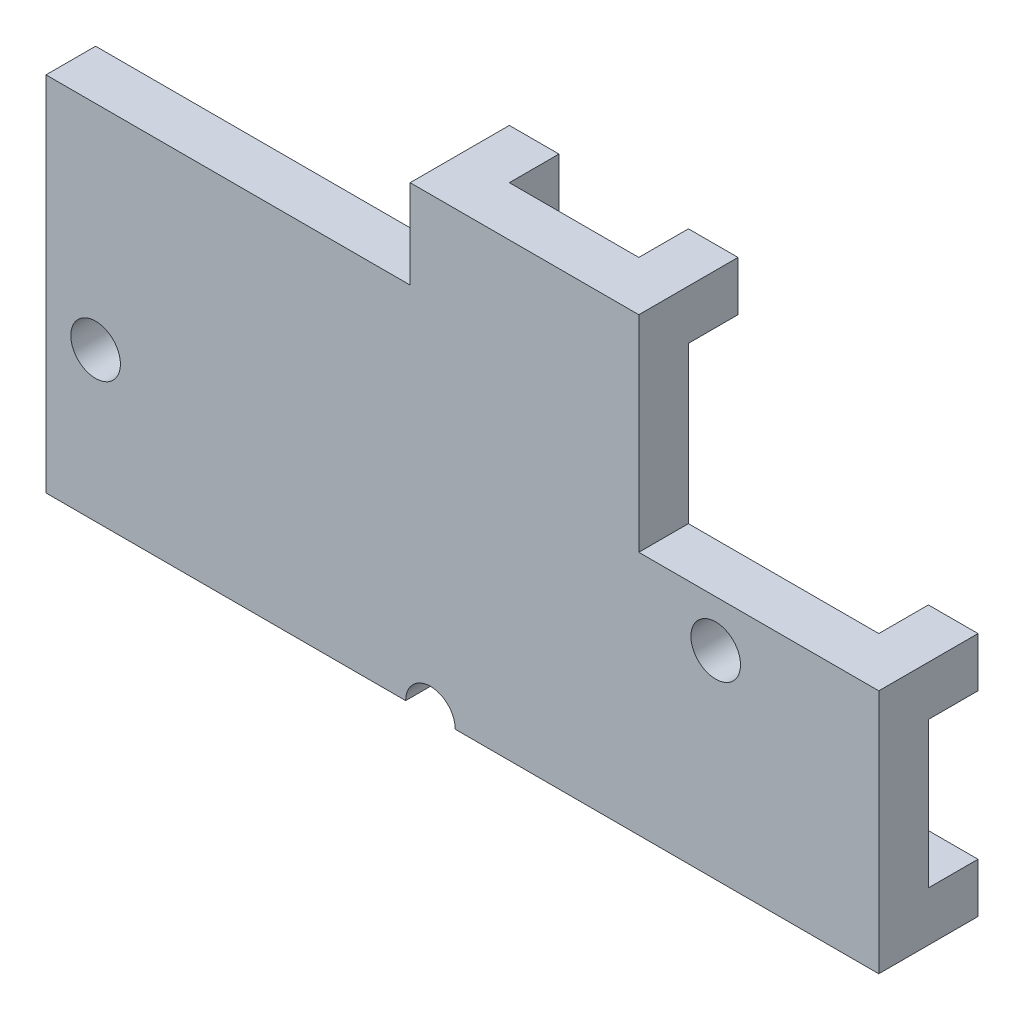
SolidWorks part; units mm, degrees
ref_plane "Front Plane" through (0, 0, 0) normal (0, 0, 1) x (1, 0, 0)
ref_plane "Top Plane" through (0, 0, 0) normal (0, 1, 0) x (1, 0, 0)
ref_plane "Right Plane" through (0, 0, 0) normal (1, 0, 0) x (0, 0, -1)
sketch "Sketch1" plane through (0, 0, 0) normal (0, 0, 1) x (1, 0, 0)
  line L1 (80.5727, -2.7261) -> (95.5727, -2.7261)
  line L2 (80.5727, -2.7261) -> (80.5727, -10.0261)
  line L3 (80.5727, -10.0261) -> (95.5727, -10.0261)
  line L4 (95.5727, -2.7261) -> (95.5727, -10.0261)
  dimension "D1" = 7.3
  dimension "D2" = 15
extrude "Boss-Extrude1" add sketch "Sketch1" along normal blind 1
sketch "Sketch2" plane through (0, 0, 1) normal (0, 0, 1) x (1, 0, 0)
  line L1 (95.5727, -2.7261) -> (92.5227, -2.7261)
  line L2 (95.5727, -2.7261) -> (95.5727, -5.0861)
  line L3 (95.5727, -5.0861) -> (92.5227, -5.0861)
  line L4 (92.5227, -2.7261) -> (92.5227, -5.0861)
extrude "Cut-Extrude1" cut sketch "Sketch2" against normal blind 1
sketch "Sketch5" plane through (95.5727, 0, 0) normal (1, 0, 0) x (0, 0, -1)
  line L1 (0, -10.0261) -> (-1, -10.0261)
  line L2 (0, -10.0261) -> (0, -5.0861)
  line L3 (0, -5.0861) -> (-1, -5.0861)
  line L4 (-1, -10.0261) -> (-1, -5.0861)
extrude ":ength-Extrude" add sketch "Sketch5" along normal blind 1.7874
sketch "Sketch6" plane through (0, -2.7261, 0) normal (0, 1, 0) x (1, 0, 0)
  line L0 (92.5227, -1) -> (80.5727, -1) construction
  line L1 (92.5227, 0) -> (87.9127, 0)
  line L2 (92.5227, 0) -> (92.5227, -1)
  line L3 (92.5227, -1) -> (87.9127, -1)
  line L4 (87.9127, 0) -> (87.9127, -1)
extrude "Height-Extrude" add sketch "Sketch6" along normal blind 1.7874
sketch "Screws" plane through (0, 0, 0) normal (0, 0, -1) x (-1, 0, 0)
  line L0 (-80.5727, -10.0261) -> (-97.3601, -10.0261) construction
  line L2 (-80.5727, -2.7261) -> (-80.5727, -10.0261) construction
  line L5 (-87.9127, -2.7261) -> (-80.5727, -2.7261) construction
  line L9 (-80.5727, -10.0261) -> (-97.3601, -10.0261) construction
  line L10 (-80.5727, -2.7261) -> (-80.5727, -10.0261) construction
  circle A0 centre (-81.5727, -7.0261) radius 0.5
  circle A1 centre (-88.3227, -10.0261) radius 0.5
  circle A2 centre (-94.0727, -6.0261) radius 0.5
  dimension "D1" = 1
  dimension "D2" = 1
  dimension "D3" = 3
  dimension "D5" = 7.3
  dimension "D4" = 1
  dimension "D6" = 7.75
  dimension "D7" = 1
  dimension "D8" = 13.5
  dimension "D9" = 4
extrude "Cut-Extrude2" cut sketch "Screws" against normal blind 1
sketch "Sketch8" plane through (0, 0, 0) normal (0, 0, -1) x (-1, 0, 0)
  line L1 (-91.5227, -1.9387) -> (-92.5227, -1.9387)
  line L2 (-91.5227, -1.9387) -> (-91.5227, -0.9387)
  line L3 (-91.5227, -0.9387) -> (-92.5227, -0.9387)
  line L4 (-92.5227, -1.9387) -> (-92.5227, -0.9387)
  line L5 (-87.9127, -1.9387) -> (-88.9127, -1.9387)
  line L6 (-87.9127, -1.9387) -> (-87.9127, -0.9387)
  line L7 (-87.9127, -0.9387) -> (-88.9127, -0.9387)
  line L8 (-88.9127, -1.9387) -> (-88.9127, -0.9387)
  line L9 (-87.9127, -1.9387) -> (-88.9127, -0.9387) construction
  line L10 (-87.9127, -0.9387) -> (-88.9127, -1.9387) construction
  line L11 (-96.3601, -6.0861) -> (-97.3601, -6.0861)
  line L12 (-96.3601, -6.0861) -> (-96.3601, -5.0861)
  line L13 (-96.3601, -5.0861) -> (-97.3601, -5.0861)
  line L14 (-97.3601, -6.0861) -> (-97.3601, -5.0861)
  line L15 (-96.3601, -9.0261) -> (-97.3601, -9.0261)
  line L16 (-96.3601, -9.0261) -> (-96.3601, -10.0261)
  line L17 (-96.3601, -10.0261) -> (-97.3601, -10.0261)
  line L18 (-97.3601, -9.0261) -> (-97.3601, -10.0261)
  line L23 (-87.9127, -0.9387) -> (-87.9127, -2.7261) construction
  point P5 (-88.4127, -1.4387)
  point P21 (0, 0)
  point P22 (0, 0)
  point P24 (0, 0)
  point P26 (0, 0)
  point P27 (0, 0)
extrude "Pins" add sketch "Sketch8" along normal blind 1
